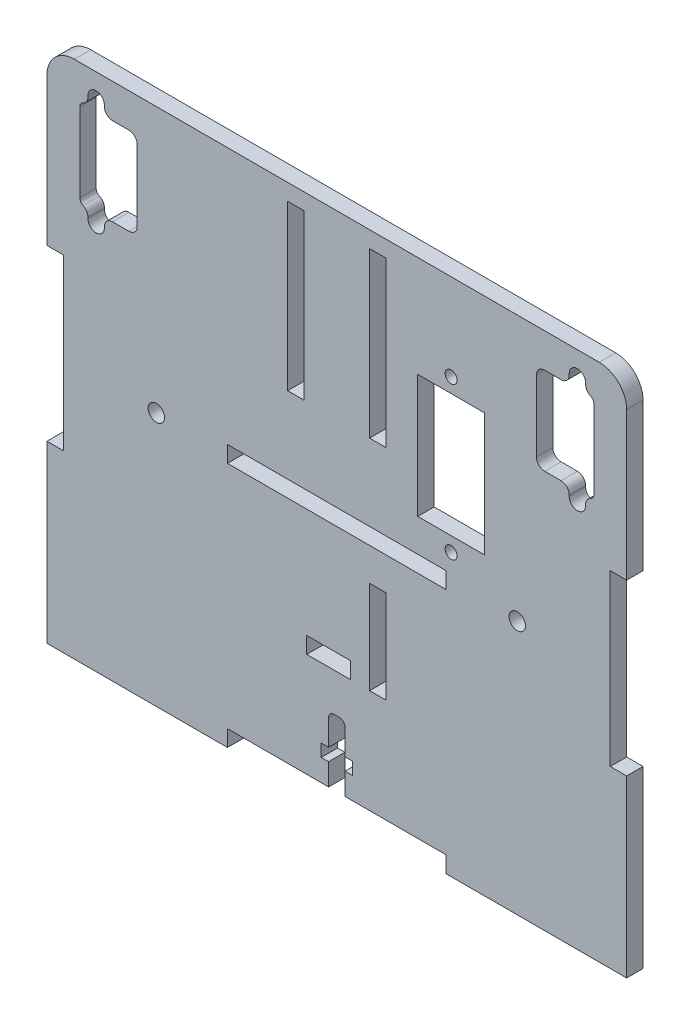
SolidWorks part; units mm, degrees
other "Marcação1"
sketch "Esboço7" plane through (-68, 31.5, 3) normal (-0.6758, 0.2828, 0.6807) x (0.7271, 0.1043, 0.6785)
sketch "Esboço8" plane through (-68, 31.5, 3) normal (-0.6758, 0.2828, 0.6807) x (0.7271, 0.1043, 0.6785)
sketch "Esboço9" plane through (-60.5, 31.5, 3) normal (-0.6758, 0.2828, 0.6807) x (0.7271, 0.1043, 0.6785)
sketch "Esboço11" plane through (-60.5, 31.5, 3) normal (-0.6758, 0.2828, 0.6807) x (0.7271, 0.1043, 0.6785)
sketch "Esboço13" plane through (-60.5, 36.25, 3) normal (-0.6758, 0.2828, 0.6807) x (0.7271, 0.1043, 0.6785)
sketch "Esboço14" plane through (-60.5, 36.25, 3) normal (-0.6758, 0.2828, 0.6807) x (0.7271, 0.1043, 0.6785)
sketch "Esboço17" plane through (-60.5, 36.25, 3) normal (-0.6758, 0.2828, 0.6807) x (0.7271, 0.1043, 0.6785)
sketch "Esboço18" plane through (-60.5, 51.25, 3) normal (-0.6758, 0.2828, 0.6807) x (0.7271, 0.1043, 0.6785)
sketch "Esboço19" plane through (-60.5, 51.25, 3) normal (-0.6758, 0.2828, 0.6807) x (0.7271, 0.1043, 0.6785)
sketch "Esboço20" plane through (-60.5, 51.25, 3) normal (-0.6758, 0.2828, 0.6807) x (0.7271, 0.1043, 0.6785)
material "Acrylic (Medium-high impact)"
ref_plane "Plano frontal" through (0, 0, 0) normal (0, 0, 1) x (1, 0, 0)
ref_plane "Plano superior" through (0, 0, 0) normal (0, 1, 0) x (1, 0, 0)
ref_plane "Plano direito" through (0, 0, 0) normal (1, 0, 0) x (0, 0, -1)
sketch "Esboço1" plane through (0, 0, 0) normal (0, 0, 1) x (1, 0, 0)
  line L1 (-50, -47.5) -> (50, -47.5)
  line L2 (-50, -47.5) -> (-50, 47.5)
  line L3 (-50, 47.5) -> (50, 47.5)
  line L4 (50, -47.5) -> (50, 47.5)
  line L5 (-50, -47.5) -> (50, 47.5) construction
  line L6 (-50, 47.5) -> (50, -47.5) construction
  point P0 (0, 0)
  dimension "D1" = 100
  dimension "D2" = 95
extrude "Ressalto-extrusão1" add sketch "Esboço1" along normal mid plane 3
sketch "Esboço2" plane through (0, 0, 1.5) normal (0, 0, 1) x (1, 0, 0)
  line L1 (-20, -47.5) -> (20, -47.5)
  line L2 (-20, -47.5) -> (-20, -44.5)
  line L3 (-20, -44.5) -> (20, -44.5)
  line L4 (20, -47.5) -> (20, -44.5)
  line L6 (-50, -47.5) -> (50, -47.5) construction
  line L7 (0, -55) -> (0, 55) construction
  line L21 (-20, 0.5) -> (20, 0.5)
  line L22 (-20, 0.5) -> (-20, -2.5)
  line L23 (-20, -2.5) -> (20, -2.5)
  line L24 (20, 0.5) -> (20, -2.5)
  line L25 (-20, 0.5) -> (20, -2.5) construction
  line L26 (-20, -2.5) -> (20, 0.5) construction
  circle A2 centre (-33, -1) radius 1.5
  circle A4 centre (33, -1) radius 1.5
  point P6 (0, -44.5)
  point P14 (0, -1)
  dimension "D4" = 3
  dimension "D8" = 3
  dimension "D5" = 13
  dimension "D2" = 40
  dimension "D3" = 45
  dimension "D6" = 3
  dimension "D13" = 40
extrude "Corte-extrusão1" cut sketch "Esboço2" against normal through all
sketch "Esboço3" plane through (0, 0, 1.5) normal (0, 0, 1) x (1, 0, 0)
  line L0 (-50, 47.5) -> (-50, -47.5) construction
  line L1 (-50, -15.5) -> (-53, -15.5)
  line L2 (-50, -15.5) -> (-50, -47.5)
  line L3 (-50, -47.5) -> (-53, -47.5)
  line L4 (-53, -15.5) -> (-53, -47.5)
  line L5 (0, -55) -> (0, 55) construction
  line L6 (50, -47.5) -> (53, -47.5)
  line L7 (50, -15.5) -> (53, -15.5)
  line L8 (50, -15.5) -> (50, -47.5)
  line L9 (53, -15.5) -> (53, -47.5)
  line L10 (-50, -47.5) -> (-20, -47.5) construction
  line L11 (50, 47.5) -> (-50, 47.5) construction
  line L16 (-53, 15.5) -> (-53, 47.5)
  line L17 (-50, 47.5) -> (-53, 47.5)
  line L18 (-50, 15.5) -> (-50, 47.5)
  line L19 (-50, 15.5) -> (-53, 15.5)
  line L20 (50, -47.5) -> (50, 47.5) construction
  line L21 (50, 15.5) -> (53, 15.5)
  line L22 (50, 15.5) -> (50, 47.5)
  line L23 (50, 47.5) -> (53, 47.5)
  line L24 (53, 15.5) -> (53, 47.5)
  line L25 (93.1741, 0) -> (-93.1741, 0) construction
  line L26 (0, -62.7565) -> (0, 62.7565) construction
  point P31 (0, 0)
  point P38 (0, 0)
  dimension "D1" = 3
  dimension "D2" = 31
  dimension "D4" = 3
  dimension "D5" = 53
extrude "Ressalto-extrusão2" add sketch "Esboço3" against normal through all
sketch "Sketch1" plane through (0, 0, -1.5) normal (0, 0, -1) x (-1, 0, 0)
  line L1 (-50.5, 33.25) -> (-36.5, 33.25) construction
  line L6 (-49, 41.25) -> (-47, 41.25) construction
  line L12 (-50.5, 39.75) -> (-50.5, 26.75) construction
  line L14 (-49, 25.25) -> (-47, 25.25) construction
  line L15 (-36.5, 39.75) -> (-36.5, 26.75)
  line L16 (-45.5, 23.5) -> (-45.5, 23.75)
  line L17 (-42.5, 23.5) -> (-42.5, 23.75)
  line L18 (-41, 25.25) -> (-38, 25.25)
  line L19 (-45.5, 43) -> (-45.5, 42.75)
  line L20 (-42.5, 43) -> (-42.5, 42.75)
  line L21 (-41, 41.25) -> (-38, 41.25)
  line L22 (-53, 47.5) -> (53, 47.5) construction
  line L24 (0, 55) -> (0, -55) construction
  line L46 (-47, 40.4587) -> (-47, 26.0413)
  line L47 (-50, -15.5) -> (-50, 15.5) construction
  line L48 (49, 25.25) -> (47, 25.25) construction
  line L49 (50.5, 39.75) -> (50.5, 26.75) construction
  line L50 (49, 41.25) -> (47, 41.25) construction
  line L51 (50.5, 33.25) -> (36.5, 33.25) construction
  line L52 (47, 40.4587) -> (47, 26.0413)
  line L53 (41, 41.25) -> (38, 41.25)
  line L54 (42.5, 43) -> (42.5, 42.75)
  line L55 (45.5, 43) -> (45.5, 42.75)
  line L56 (41, 25.25) -> (38, 25.25)
  line L57 (42.5, 23.5) -> (42.5, 23.75)
  line L58 (45.5, 23.5) -> (45.5, 23.75)
  line L59 (36.5, 39.75) -> (36.5, 26.75)
  arc A0 (-42.5, 43) -> (-45.5, 43) centre (-44, 43) ccw
  arc A1 (-45.5, 23.5) -> (-42.5, 23.5) centre (-44, 23.5) ccw
  arc A2 (-42.5, 23.75) -> (-41, 25.25) centre (-41, 23.75) cw
  arc A3 (-45.5, 23.75) -> (-46.4, 25.1248) centre (-47, 23.75) ccw
  arc A4 (-42.5, 42.75) -> (-41, 41.25) centre (-41, 42.75) ccw
  arc A5 (-45.5, 42.75) -> (-46.4, 41.3752) centre (-47, 42.75) cw
  arc A6 (-50.5, 26.75) -> (-49, 25.25) centre (-49, 26.75) ccw construction
  arc A7 (-38, 25.25) -> (-36.5, 26.75) centre (-38, 26.75) ccw
  arc A8 (-38, 41.25) -> (-36.5, 39.75) centre (-38, 39.75) cw
  arc A9 (-49, 41.25) -> (-50.5, 39.75) centre (-49, 39.75) ccw construction
  arc A30 (-47, 26.0413) -> (-46.4, 25.1248) centre (-46, 26.0413) ccw
  arc A31 (-47, 40.4587) -> (-46.4, 41.3752) centre (-46, 40.4587) cw
  arc A32 (49, 41.25) -> (50.5, 39.75) centre (49, 39.75) cw construction
  arc A33 (50.5, 26.75) -> (49, 25.25) centre (49, 26.75) cw construction
  arc A34 (47, 40.4587) -> (46.4, 41.3752) centre (46, 40.4587) ccw
  arc A35 (47, 26.0413) -> (46.4, 25.1248) centre (46, 26.0413) cw
  arc A36 (38, 41.25) -> (36.5, 39.75) centre (38, 39.75) ccw
  arc A37 (38, 25.25) -> (36.5, 26.75) centre (38, 26.75) cw
  arc A38 (45.5, 42.75) -> (46.4, 41.3752) centre (47, 42.75) ccw
  arc A39 (42.5, 42.75) -> (41, 41.25) centre (41, 42.75) cw
  arc A40 (45.5, 23.75) -> (46.4, 25.1248) centre (47, 23.75) cw
  arc A41 (42.5, 23.75) -> (41, 25.25) centre (41, 23.75) ccw
  arc A42 (45.5, 23.5) -> (42.5, 23.5) centre (44, 23.5) cw
  arc A43 (42.5, 43) -> (45.5, 43) centre (44, 43) cw
  point P8 (-42.5, 25.25)
  point P21 (-45.5, 25.25)
  point P24 (-42.5, 41.25)
  point P29 (-50.5, 25.25)
  point P34 (-36.5, 41.25)
  point P37 (-50.5, 41.25)
  point P127 (50.5, 41.25)
  point P128 (36.5, 41.25)
  point P129 (50.5, 25.25)
  point P130 (42.5, 41.25)
  point P131 (45.5, 25.25)
  point P132 (42.5, 25.25)
  dimension "D1" = 16
  dimension "D3" = 3
  dimension "D5" = 1.5
  dimension "D6" = 1.5
  dimension "D7" = 3
  dimension "D8" = 3
  dimension "D9" = 5
  dimension "D4" = 19.5
  dimension "D18" = 1
  dimension "D20" = 7.5
extrude "Cut-Extrude1" cut sketch "Sketch1" against normal through all both and the other way through all
sketch "Sketch2" plane through (0, 0, 0) normal (0, 0, 1) x (1, 0, 0)
  line L0 (20, -44.5) -> (-20, -44.5) construction
  line L1 (-0.5, -32.5) -> (0.5, -32.5)
  line L2 (-1.5, -33.5) -> (-1.5, -38.23)
  line L3 (-1.5, -44.5) -> (1.5, -44.5)
  line L4 (1.5, -33.5) -> (1.5, -38.23)
  line L5 (1.5, -38.23) -> (2.85, -38.23)
  line L6 (-2.85, -38.23) -> (-1.5, -38.23)
  line L7 (-2.85, -38.23) -> (-2.85, -40.5)
  line L8 (-2.85, -40.5) -> (-1.5, -40.5)
  line L9 (2.85, -38.23) -> (2.85, -40.5)
  line L10 (-1.5, -40.5) -> (-1.5, -44.5)
  line L11 (1.5, -40.5) -> (2.85, -40.5)
  line L12 (1.5, -40.5) -> (1.5, -44.5)
  arc A0 (0.5, -32.5) -> (1.5, -33.5) centre (0.5, -33.5) cw
  arc A1 (-0.5, -32.5) -> (-1.5, -33.5) centre (-0.5, -33.5) ccw
  point P6 (0, -32.5)
  point P18 (1.5, -32.5)
  point P21 (-1.5, -32.5)
  dimension "D7" = 1
  dimension "D1" = 3
  dimension "D2" = 12
  dimension "D3" = 2.27
  dimension "D4" = 1.35
  dimension "D5" = 1.35
  dimension "D6" = 4
extrude "Cut-Extrude4" cut sketch "Sketch2" against normal through all both and the other way through all
fillet "Fillet1" radius 5 2 edges at (53, 47.5, 0) (-53, 47.5, 0)
sketch "Sketch3" plane through (0, 0, 0) normal (0, 0, 1) x (1, 0, 0)
  line L0 (-20, -2.5) -> (20, -2.5) construction
  line L1 (9, 44.5) -> (6, 44.5)
  line L2 (9, 44.5) -> (9, 14.5)
  line L3 (9, 14.5) -> (6, 14.5)
  line L4 (6, 44.5) -> (6, 14.5)
  line L5 (6, -8.5) -> (9, -8.5)
  line L6 (0, -1.65) -> (0, 1.65) construction
  line L7 (-6, 44.5) -> (-6, 14.5)
  line L8 (-9, 14.5) -> (-6, 14.5)
  line L9 (-9, 44.5) -> (-9, 14.5)
  line L10 (-9, 44.5) -> (-6, 44.5)
  line L11 (48, 47.5) -> (-48, 47.5) construction
  line L12 (20, 0.5) -> (-20, 0.5) construction
  line L21 (6, -8.5) -> (6, -25.5)
  line L22 (6, -25.5) -> (9, -25.5)
  line L23 (9, -8.5) -> (9, -25.5)
  line L28 (-5.5, -22.5) -> (2.5, -22.5)
  line L29 (-5.5, -22.5) -> (-5.5, -25.5)
  line L30 (-5.5, -25.5) -> (2.5, -25.5)
  line L31 (2.5, -22.5) -> (2.5, -25.5)
  dimension "D1" = 3
  dimension "D2" = 30
  dimension "D3" = 3
  dimension "D4" = 6
  dimension "D5" = 17
  dimension "D6" = 6
  dimension "D7" = 8
  dimension "D8" = 3.5
  dimension "D9" = 20
  dimension "D10" = 14
extrude "Cut-Extrude5" cut sketch "Sketch3" against normal through all both and the other way through all
sketch "Sketch4" plane through (0, 0, 1.5) normal (0, 0, 1) x (1, 0, 0)
  line L0 (20, 0.5) -> (-20, 0.5) construction
  line L1 (14.8, 29) -> (27, 29)
  line L2 (14.8, 29) -> (14.8, 6.5)
  line L3 (14.8, 6.5) -> (27, 6.5)
  line L4 (27, 29) -> (27, 6.5)
  line L8 (50, -15.5) -> (50, 15.5) construction
  circle A0 centre (20.9, 31.65) radius 1.1
  circle A1 centre (20.9, 3.85) radius 1.1
  dimension "D5" = 2.2
  dimension "D1" = 12.2
  dimension "D2" = 22.5
  dimension "D3" = 23
  dimension "D4" = 6
extrude "Cut-Extrude6" cut sketch "Sketch4" against normal through all both and the other way through all
